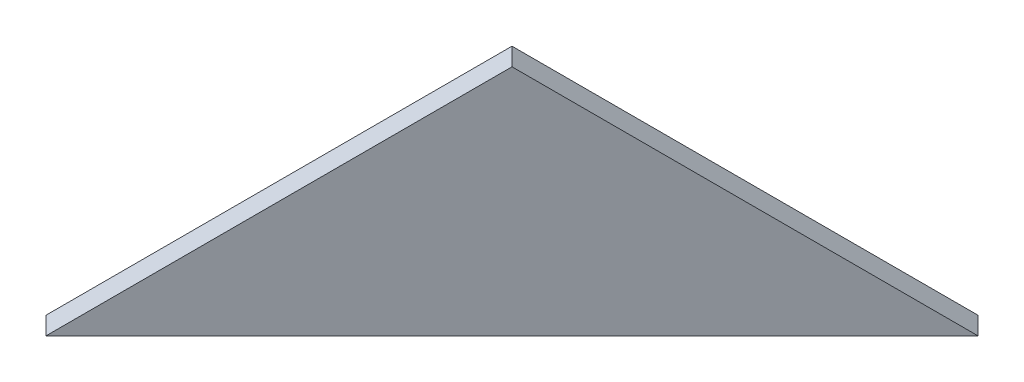
SolidWorks part; units mm, degrees
material "Acrylic (Medium-high impact)"
ref_plane "Front Plane" through (0, 0, 0) normal (0, 0, 1) x (1, 0, 0)
ref_plane "Top Plane" through (0, 0, 0) normal (0, 1, 0) x (1, 0, 0)
ref_plane "Right Plane" through (0, 0, 0) normal (1, 0, 0) x (0, 0, -1)
ref_plane "Plane1" through (80.4015, 0, 80.4015) normal (0.7071, 0, 0.7071) x (0.7071, 0, -0.7071)
sketch "Sketch1" plane through (80.4015, 0, 80.4015) normal (0.7071, 0, 0.7071) x (0.7071, 0, -0.7071)
  line L0 (0, -83.5123) -> (-39.1066, -111.1649) construction
  line L1 (-39.1066, -111.1649) -> (39.1066, -111.1649) construction
  line L2 (39.1066, -111.1649) -> (0, -83.5123) construction
  line L3 (0, -83.5123) -> (-39.1066, -111.1649)
  line L4 (-39.1066, -111.1649) -> (39.1066, -111.1649)
  line L5 (39.1066, -111.1649) -> (0, -83.5123)
extrude "Boss-Extrude1" add sketch "Sketch1" against normal mid plane 3
